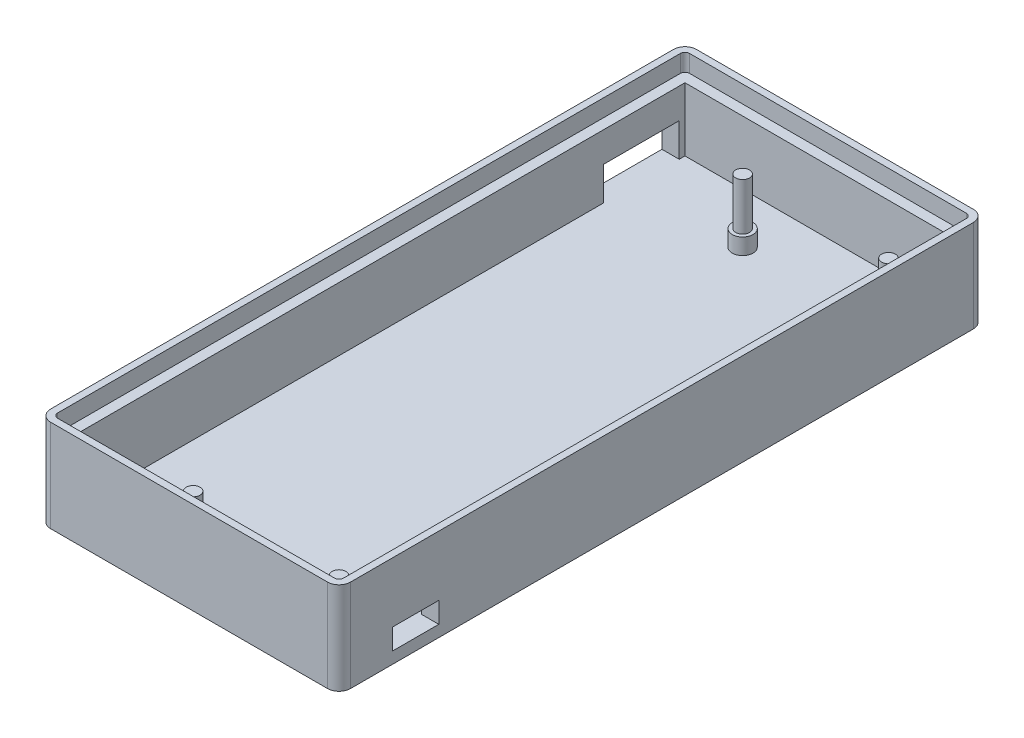
SolidWorks part; units mm, degrees
ref_plane "Front Plane" through (0, 0, 0) normal (0, 0, 1) x (1, 0, 0)
ref_plane "Top Plane" through (0, 0, 0) normal (0, 1, 0) x (1, 0, 0)
ref_plane "Right Plane" through (0, 0, 0) normal (1, 0, 0) x (0, 0, -1)
sketch "Sketch1" plane through (0, 0, 0) normal (0, 1, 0) x (1, 0, 0)
  line L1 (-77.0226, 53.0801) -> (-27.0226, 53.0801)
  line L2 (-77.0226, 53.0801) -> (-77.0226, -56.9199)
  line L3 (-77.0226, -56.9199) -> (-27.0226, -56.9199)
  line L4 (-27.0226, 53.0801) -> (-27.0226, -56.9199)
  dimension "D1" = 110
  dimension "D2" = 50
extrude "Boss-Extrude1" add sketch "Sketch1" along normal blind 2
sketch "Sketch2" plane through (0, 2, 0) normal (0, 1, 0) x (1, 0, 0)
  line L0 (-75.0226, 51.0801) -> (-75.0226, -54.9199)
  line L1 (-77.0226, 53.0801) -> (-27.0226, 53.0801)
  line L2 (-77.0226, 53.0801) -> (-77.0226, -56.9199)
  line L3 (-77.0226, -56.9199) -> (-27.0226, -56.9199)
  line L4 (-27.0226, 53.0801) -> (-27.0226, -56.9199)
  line L5 (-75.0226, -54.9199) -> (-29.0226, -54.9199)
  line L6 (-29.0226, 51.0801) -> (-29.0226, -54.9199)
  line L7 (-75.0226, 51.0801) -> (-29.0226, 51.0801)
  dimension "D1" = 2
extrude "Boss-Extrude3" add sketch "Sketch2" along normal blind 11
sketch "Sketch3" plane through (0, 2, 0) normal (0, 1, 0) x (1, 0, 0)
  circle A0 centre (-31.0226, 42.3801) radius 1.2
  circle A1 centre (-31.0226, -52.9199) radius 1.2
  circle A2 centre (-56.3226, 42.3801) radius 1.2
  circle A3 centre (-56.3226, -52.9199) radius 1.2
extrude "Boss-Extrude4" add sketch "Sketch3" along normal blind 11
sketch "Sketch4" plane through (0, 13, 0) normal (0, 1, 0) x (1, 0, 0)
  line L8 (-26.0226, 54.0801) -> (-78.0226, 54.0801)
  line L9 (-78.0226, 54.0801) -> (-78.0226, -57.9199)
  line L10 (-78.0226, -57.9199) -> (-26.0226, -57.9199)
  line L11 (-26.0226, -57.9199) -> (-26.0226, 54.0801)
  line L12 (-26.0226, 54.0801) -> (-78.0226, 54.0801)
  line L13 (-78.0226, 54.0801) -> (-78.0226, -57.9199)
  line L14 (-78.0226, -57.9199) -> (-26.0226, -57.9199)
  line L15 (-26.0226, -57.9199) -> (-26.0226, 54.0801)
  dimension "D1" = 3
extrude "Extrude-Thin1" add sketch "Sketch4" against normal blind 13 thin thin type one direction reverse wall 1
fillet "Fillet2" radius 2 4 edges at (-78.0226, 6.5, -54.0801) (-26.0226, 6.5, -54.0801) (-26.0226, 6.5, 57.9199) (-78.0226, 6.5, 57.9199)
sketch "Sketch5" plane through (0, 13, 0) normal (0, 1, 0) x (1, 0, 0)
  line L8 (-28.0226, 52.8801) -> (-76.0226, 52.8801)
  line L9 (-76.8226, 52.0801) -> (-76.8226, -55.9199)
  line L10 (-76.0226, -56.7199) -> (-28.0226, -56.7199)
  line L11 (-27.2226, -55.9199) -> (-27.2226, 52.0801)
  line L12 (-28.0226, 52.8801) -> (-76.0226, 52.8801)
  line L13 (-76.8226, 52.0801) -> (-76.8226, -55.9199)
  line L14 (-76.0226, -56.7199) -> (-28.0226, -56.7199)
  line L15 (-27.2226, -55.9199) -> (-27.2226, 52.0801)
  arc A8 (-76.0226, 52.8801) -> (-76.8226, 52.0801) centre (-76.0226, 52.0801) ccw
  arc A9 (-76.8226, -55.9199) -> (-76.0226, -56.7199) centre (-76.0226, -55.9199) ccw
  arc A10 (-28.0226, -56.7199) -> (-27.2226, -55.9199) centre (-28.0226, -55.9199) ccw
  arc A11 (-27.2226, 52.0801) -> (-28.0226, 52.8801) centre (-28.0226, 52.0801) ccw
  arc A12 (-76.0226, 52.8801) -> (-76.8226, 52.0801) centre (-76.0226, 52.0801) ccw
  arc A13 (-76.8226, -55.9199) -> (-76.0226, -56.7199) centre (-76.0226, -55.9199) ccw
  arc A14 (-28.0226, -56.7199) -> (-27.2226, -55.9199) centre (-28.0226, -55.9199) ccw
  arc A15 (-27.2226, 52.0801) -> (-28.0226, 52.8801) centre (-28.0226, 52.0801) ccw
  dimension "D1" = 1.2
extrude "Extrude-Thin3" add sketch "Sketch5" along normal blind 3 thin
sketch "Sketch6" plane through (0, 2, 0) normal (0, 1, 0) x (1, 0, 0)
  circle A0 centre (-56.3226, -52.9199) radius 1.8
  circle A1 centre (-31.0226, -52.9199) radius 1.8
  circle A2 centre (-56.3226, 42.3801) radius 1.8
  circle A3 centre (-31.0226, 42.3801) radius 1.8
extrude "Boss-Extrude5" add sketch "Sketch6" along normal blind 2.8
sketch "Sketch7" plane through (0, 2, 0) normal (0, 1, 0) x (1, 0, 0)
  line L0 (-31.0226, -52.9199) -> (-31.0226, -48.6199)
  line L1 (-31.0226, -48.6199) -> (-18.3371, -48.6199)
sketch "Sketch8" plane through (-26.0226, 0, 0) normal (1, 0, 0) x (0, 0, -1)
  line L0 (-52.9199, 2) -> (-48.6199, 2) construction
  line L2 (-48.6199, 2) -> (-40.6199, 2)
  line L3 (-48.6199, 2) -> (-48.6199, 5.6)
  line L4 (-48.6199, 5.6) -> (-40.6199, 5.6)
  line L5 (-40.6199, 2) -> (-40.6199, 5.6)
  dimension "D1" = 8
  dimension "D2" = 3.6
extrude "Cut-Extrude2" cut sketch "Sketch8" against normal blind 12.8
sketch "Sketch11" plane through (-78.0226, 0, 0) normal (-1, 0, 0) x (0, 0, 1)
  line L0 (-51.0801, 2) -> (54.9199, 2) construction
  line L1 (-50.0801, 7.8) -> (-36.9801, 7.8)
  line L2 (-50.0801, 7.8) -> (-50.0801, 2)
  line L3 (-50.0801, 2) -> (-36.9801, 2)
  line L4 (-36.9801, 7.8) -> (-36.9801, 2)
  line L5 (-51.0801, 13) -> (-51.0801, 2) construction
  dimension "D1" = 5.8
  dimension "D2" = 13.1
  dimension "D3" = 0
  dimension "D4" = 1
extrude "Cut-Extrude5" cut sketch "Sketch11" against normal blind 3
